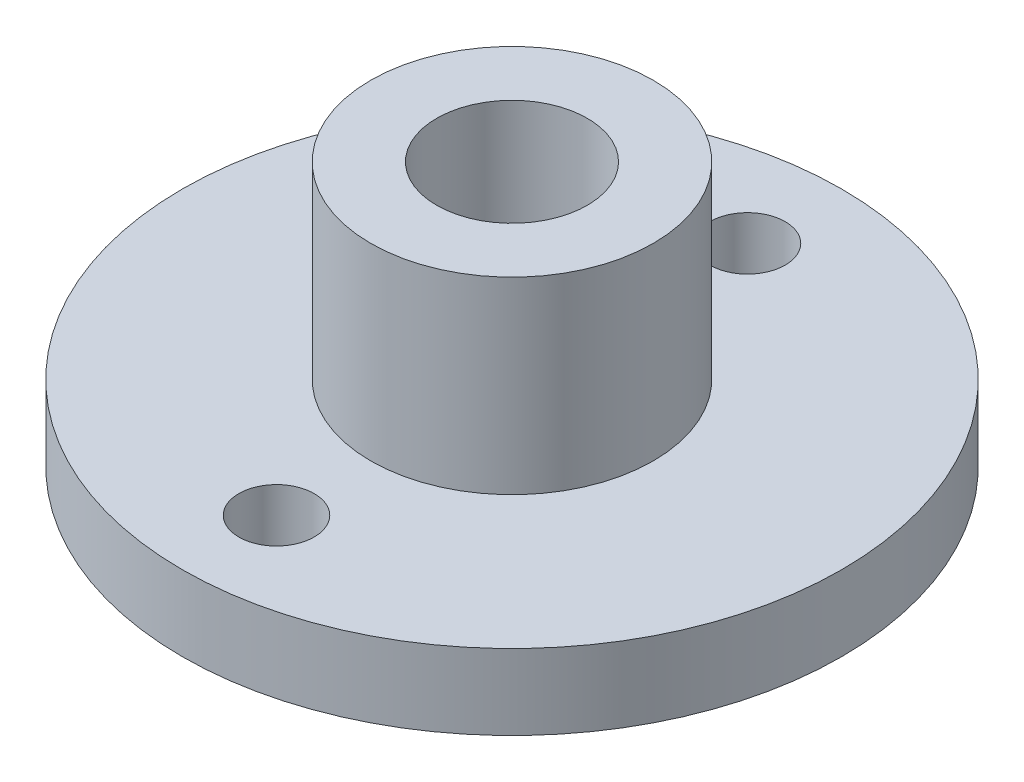
SolidWorks part; units mm, degrees
material "AISI 1020"
ref_plane "Front Plane" through (0, 0, 0) normal (0, 0, 1) x (1, 0, 0)
ref_plane "Top Plane" through (0, 0, 0) normal (0, 1, 0) x (1, 0, 0)
ref_plane "Right Plane" through (0, 0, 0) normal (1, 0, 0) x (0, 0, -1)
sketch "Sketch1" plane through (0, 0, 0) normal (0, 1, 0) x (1, 0, 0)
  circle A0 centre (0, 0) radius 17.5
  circle A2 centre (0, 12.5) radius 2
  circle A3 centre (0, -12.5) radius 2
  dimension "D1" = 35
  dimension "D3" = 2
  dimension "D4" = 2
  dimension "D5" = 12.5
  dimension "D6" = 12.5
extrude "Boss-Extrude1" add sketch "Sketch1" along normal blind 4
sketch "Sketch2" plane through (0, 4, 0) normal (0, 1, 0) x (1, 0, 0)
  circle A0 centre (0, 0) radius 7.5
  circle A1 centre (0, 0) radius 4
  dimension "D1" = 15
  dimension "D2" = 8
extrude "Boss-Extrude2" add sketch "Sketch2" along normal blind 10
sketch "Sketch3" plane through (0, 0, 0) normal (0, -1, 0) x (1, 0, 0)
  line L1 (0, 17.5) -> (0, -17.5) construction
  circle A1 centre (0, 0) radius 17.5 construction
  point P5 (0, 0)
